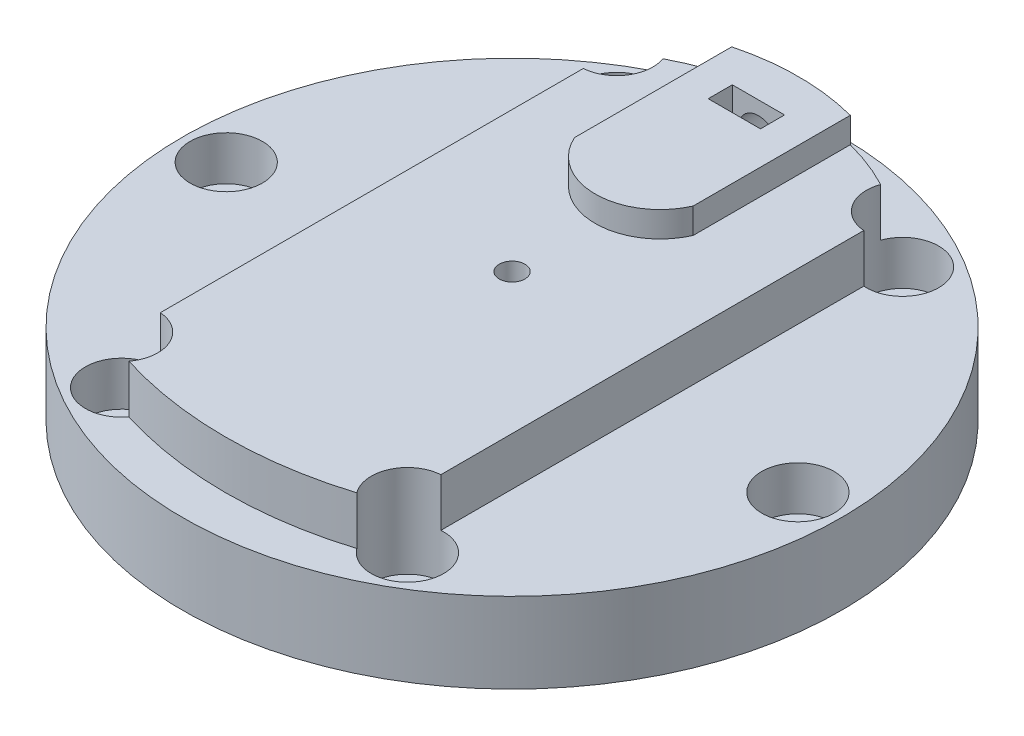
SolidWorks part; units mm, degrees
ref_plane "Front Plane" through (0, 0, 0) normal (0, 0, 1) x (1, 0, 0)
ref_plane "Top Plane" through (0, 0, 0) normal (0, 1, 0) x (1, 0, 0)
ref_plane "Right Plane" through (0, 0, 0) normal (1, 0, 0) x (0, 0, -1)
sketch "Sketch1" plane through (0, 0, 0) normal (0, 1, 0) x (1, 0, 0)
  line L0 (-17.45, 28.5) -> (-17.45, 32)
  line L5 (-21.25, 28.5) -> (21.25, 28.5)
  line L6 (-21.25, 28.5) -> (-21.25, -28.5)
  line L7 (-21.25, -28.5) -> (21.25, -28.5) construction
  line L8 (21.25, 28.5) -> (21.25, -28.5)
  line L9 (-21.25, 28.5) -> (21.25, -28.5) construction
  line L10 (-21.25, -28.5) -> (21.25, 28.5) construction
  line L11 (-17.45, 32) -> (17.45, 32) construction
  line L12 (17.45, 32) -> (17.45, 28.5)
  line L13 (0, 32) -> (0, 28.5) construction
  arc A0 (-21.25, -28.5) -> (21.25, -28.5) centre (0, 14.1562) ccw
  arc A1 (-17.45, 32) -> (17.45, 32) centre (0, 8.6498) cw
  point P0 (0, 0)
  point P14 (0, -33.5)
  point P15 (0, 37.8)
  dimension "D6" = 5.8
  dimension "D1" = 42.5
  dimension "D2" = 57
  dimension "D3" = 34.9
  dimension "D4" = 3.5
  dimension "D5" = 5
extrude "Boss-Extrude1" add sketch "Sketch1" along normal blind 6 contours L6 A0 L8 L5 | A1 L0 L5 L12
sketch "Sketch2" plane through (0, 6, 0) normal (0, 1, 0) x (1, 0, 0)
  line L0 (0, 37.8) -> (0, 17.3) construction
  line L1 (7.375, 17.3) -> (-7.375, 17.3) construction
  line L2 (-7.375, 17.3) -> (-7.375, 37.8)
  line L3 (-7.375, 37.8) -> (7.375, 37.8)
  line L4 (7.375, 17.3) -> (7.375, 37.8)
  line L6 (-21.25, 28.5) -> (-21.25, -28.5)
  line L7 (21.25, -28.5) -> (21.25, 28.5)
  line L8 (21.25, 28.5) -> (17.45, 28.5)
  line L9 (17.45, 28.5) -> (17.45, 32)
  line L10 (-17.45, 32) -> (-17.45, 28.5)
  line L11 (-17.45, 28.5) -> (-21.25, 28.5)
  line L12 (-21.25, 28.5) -> (-21.25, -28.5) construction
  line L13 (21.25, -28.5) -> (21.25, 28.5) construction
  line L14 (21.25, 28.5) -> (17.45, 28.5) construction
  line L15 (17.45, 28.5) -> (17.45, 32) construction
  line L16 (-17.45, 32) -> (-17.45, 28.5) construction
  line L17 (-17.45, 28.5) -> (-21.25, 28.5) construction
  arc A0 (-7.375, 17.3) -> (7.375, 17.3) centre (0, 20.5657) ccw
  arc A2 (-21.25, -28.5) -> (21.25, -28.5) centre (0, 14.1562) ccw
  arc A3 (17.45, 32) -> (-17.45, 32) centre (0, 8.6498) ccw
  arc A4 (-21.25, -28.5) -> (21.25, -28.5) centre (0, 14.1562) ccw construction
  arc A5 (17.45, 32) -> (-17.45, 32) centre (0, 8.6498) ccw construction
  point P17 (0, 12.5)
  dimension "D4" = 4.8
  dimension "D2" = 7.375
  dimension "D3" = 20.5
  dimension "D1" = 0
sketch "Sketch3" plane through (0, 0, 0) normal (0, -1, 0) x (1, 0, 0)
  line L0 (-21.25, 28.5) -> (21.25, 28.5) construction
  line L1 (-17.45, -28.5) -> (-43.7157, -28.5)
  line L2 (-17.45, -28.5) -> (-17.45, 25)
  line L3 (-17.45, 25) -> (-43.7157, 25)
  line L4 (-43.7157, -28.5) -> (-43.7157, 25)
  line L5 (-21.25, -28.5) -> (-21.25, 28.5) construction
  line L6 (0, -8.6498) -> (0, 28.5) construction
  line L7 (17.45, 25) -> (43.7157, 25)
  line L8 (43.7157, -28.5) -> (43.7157, 25)
  line L9 (17.45, -28.5) -> (43.7157, -28.5)
  line L10 (17.45, -28.5) -> (17.45, 25)
  line M15 (21.25, -28.5) -> (21.25, 28.5)
  line M17 (-21.25, 28.5) -> (-21.25, -28.5)
  dimension "D1" = 53.5
extrude "Cut-Extrude2" cut sketch "Sketch3" against normal up to surface (6 mm away) contours L9 L8 L7 M15 | L4 L1 L3 M17
extrude "Boss-Extrude2" add sketch "Sketch2" along normal blind 3.175
sketch "Sketch4" plane through (0, 0, 0) normal (0, -1, 0) x (1, 0, 0)
  line L0 (17.45, -32) -> (17.45, -50.0425)
  line L1 (17.45, -50.0425) -> (-17.45, -50.0425)
  line L2 (-17.45, -50.0425) -> (-17.45, -32)
  arc A0 (-17.45, -32) -> (17.45, -32) centre (0, -8.6498) ccw construction
  arc A1 (-17.45, -32) -> (17.45, -32) centre (0, -8.6498) ccw
extrude "Cut-Extrude3" cut sketch "Sketch4" against normal up to surface (9.175 mm away) contours L2 A1 L0 L1 up to face at (0, 9.175, -26.35)
sketch "Sketch5" plane through (0, 9.175, 0) normal (0, 1, 0) x (1, 0, 0)
  line L0 (0, 37.8) -> (0, 31.3) construction
  line L2 (3.25, 29.8) -> (-3.25, 29.8)
  line L3 (3.25, 29.8) -> (3.25, 32.8)
  line L4 (3.25, 32.8) -> (-3.25, 32.8)
  line L5 (-3.25, 29.8) -> (-3.25, 32.8)
  line L6 (3.25, 29.8) -> (-3.25, 32.8) construction
  line L7 (3.25, 32.8) -> (-3.25, 29.8) construction
  arc A0 (7.375, 36.8516) -> (-7.375, 36.8516) centre (0, 8.6498) ccw construction
  dimension "D1" = 5
  dimension "D2" = 6.5
  dimension "D3" = 3
extrude "Cut-Extrude4" cut sketch "Sketch5" against normal blind 6.95 contours L3 L2 L5 L4
ref_plane "Plane1" through (0, 9.175, -37.8) normal (0, 0, -1) x (-1, 0, 0)
sketch "Sketch6" plane through (0, 9.175, -37.8) normal (0, 0, -1) x (-1, 0, 0)
  line L0 (0, 0) -> (0, -9.175) construction
  line L1 (7.375, 0) -> (-7.375, 0) construction
  circle A0 centre (0, -4.2) radius 2.5
  dimension "D2" = 5
  dimension "D1" = 4.2
extrude "Cut-Extrude5" cut sketch "Sketch6" against normal offset from surface (10 mm away) 2 contours A0 up to face at (0, 5.7, -29.8) offset beyond the face yes
sketch "Sketch7" plane through (0, 6, 0) normal (0, -1, 0) x (1, 0, 0)
  line L0 (0, -37.8) -> (0, 33.5) construction
  line L1 (10, -2.15) -> (-10, -2.15) construction
  arc A0 (-17.45, -32) -> (17.45, -32) centre (0, -8.6498) ccw construction
  arc A1 (21.25, 28.5) -> (-21.25, 28.5) centre (0, -14.1562) ccw construction
  circle A2 centre (0, -2.15) radius 4.1649
  point P15 (0, -2.15)
  dimension "D1" = 20
hole_wizard "M3 Clearance Hole1" positions "Sketch8" profile "Sketch9" hole size "M3" standard "ANSI Metric" end condition through all
sketch "Sketch8" plane through (0, 0, 0) normal (0, -1, 0) x (-1, 0, 0)
  point P0 (0, 2.15)
sketch "Sketch9" plane through (0, 0, -2.15) normal (1, 0, 0) x (0, 0, -1)
  line L0 (0, 0) -> (0, 9.175)
  line L1 (0, 9.175) -> (1.6, 9.175)
  line L2 (1.6, 9.175) -> (1.6, 0)
  line L5 (1.6, 0) -> (0, 0)
  line L11 (0, -6.35) -> (0, 107.95) construction
  dimension "Thru Hole Dia." = 3.2
  dimension "Thru Hole Depth" = 9.175
hole_wizard "M6x1.0 Tapped Hole2" [suppressed] positions "3DSketch2" profile "Sketch16" tap size "M6x1.0" standard "ANSI Metric"
sketch3d "3DSketch2"
  point P0 (-10, 6, -2.15)
  point P3 (10, 6, -2.15)
sketch "Sketch16" plane through (-10, 6, -2.15) normal (1, 0, 0) x (0, 0, 1)
  line L0 (0, 0) -> (0, 6)
  line L1 (0, 6) -> (2.5, 6)
  line L2 (2.5, 6) -> (2.5, 0)
  line L5 (2.5, 0) -> (0, 0)
  line L11 (0, -6.35) -> (0, 107.95) construction
  dimension "Thru Tap Drill Dia." = 5
  dimension "Thru Tap Drill Depth" = 6
cosmetic thread "Hole Thread4" [suppressed] parameters "D2"=6
cosmetic thread "Hole Thread5" [suppressed] parameters "D2"=6
sketch "Sketch17" plane through (0, 0, 0) normal (0, -1, 0) x (1, 0, 0)
  circle A0 centre (0, -2.15) radius 1.6 construction
  circle A1 centre (0, -2.15) radius 1.6 construction
  circle A2 centre (0, -2.15) radius 41
  dimension "D1" = 82
extrude "Boss-Extrude3" add sketch "Sketch17" along normal blind 10
sketch "Sketch18" plane through (0, -10, 0) normal (0, -1, 0) x (1, 0, 0)
  circle A0 centre (17.78, -32.9459) radius 2.5 construction
  circle A1 centre (35.56, -2.15) radius 2.5 construction
  circle A2 centre (17.78, 28.6459) radius 2.5 construction
  circle A3 centre (-17.78, -32.9459) radius 2.5 construction
  circle A4 centre (-35.56, -2.15) radius 2.5 construction
  circle A5 centre (-17.78, 28.6459) radius 2.5 construction
  circle A6 centre (17.78, -32.9459) radius 2.5
  circle A7 centre (35.56, -2.15) radius 2.5
  circle A8 centre (17.78, 28.6459) radius 2.5
  circle A9 centre (-17.78, -32.9459) radius 2.5
  circle A10 centre (-35.56, -2.15) radius 2.5
  circle A11 centre (-17.78, 28.6459) radius 2.5
extrude "Cut-Extrude6" cut sketch "Sketch18" against normal blind 5
sketch "Sketch19" plane through (0, 6, 0) normal (0, 1, 0) x (1, 0, 0)
  circle A0 centre (-17.78, 32.9459) radius 2.5 construction
  circle A1 centre (17.78, 32.9459) radius 2.5 construction
  circle A2 centre (35.56, 2.15) radius 2.5 construction
  circle A3 centre (17.78, -28.6459) radius 2.5 construction
  circle A4 centre (-35.56, 2.15) radius 2.5 construction
  circle A5 centre (-17.78, -28.6459) radius 2.5 construction
  circle A6 centre (-17.78, 32.9459) radius 2.5 construction
  circle A7 centre (17.78, 32.9459) radius 2.5 construction
  circle A8 centre (35.56, 2.15) radius 2.5 construction
  circle A9 centre (17.78, -28.6459) radius 2.5 construction
  circle A10 centre (-35.56, 2.15) radius 2.5 construction
  circle A11 centre (-17.78, -28.6459) radius 2.5 construction
  circle A12 centre (-17.78, 32.9459) radius 4.5
  circle A13 centre (17.78, 32.9459) radius 4.5
  circle A14 centre (35.56, 2.15) radius 4.5
  circle A15 centre (17.78, -28.6459) radius 4.5
  circle A16 centre (-17.78, -28.6459) radius 4.5
  circle A17 centre (-35.56, 2.15) radius 4.5
  dimension "D1" = 9
extrude "Cut-Extrude7" cut sketch "Sketch19" against normal offset from surface (11.5 mm away) 5.5 up to face at (0, 0, -43.15) offset beyond the face yes
sketch "Sketch20" plane through (0, 6, 0) normal (0, 1, 0) x (1, 0, 0)
  circle A0 centre (-20.5814, -26.5803) radius 2.7063
  circle A1 centre (20.2136, -26.5803) radius 3.317
extrude "Cut-Extrude8" cut sketch "Sketch20" against normal up to surface (6 mm away) up to face at (-35.56, 0, -6.65)
